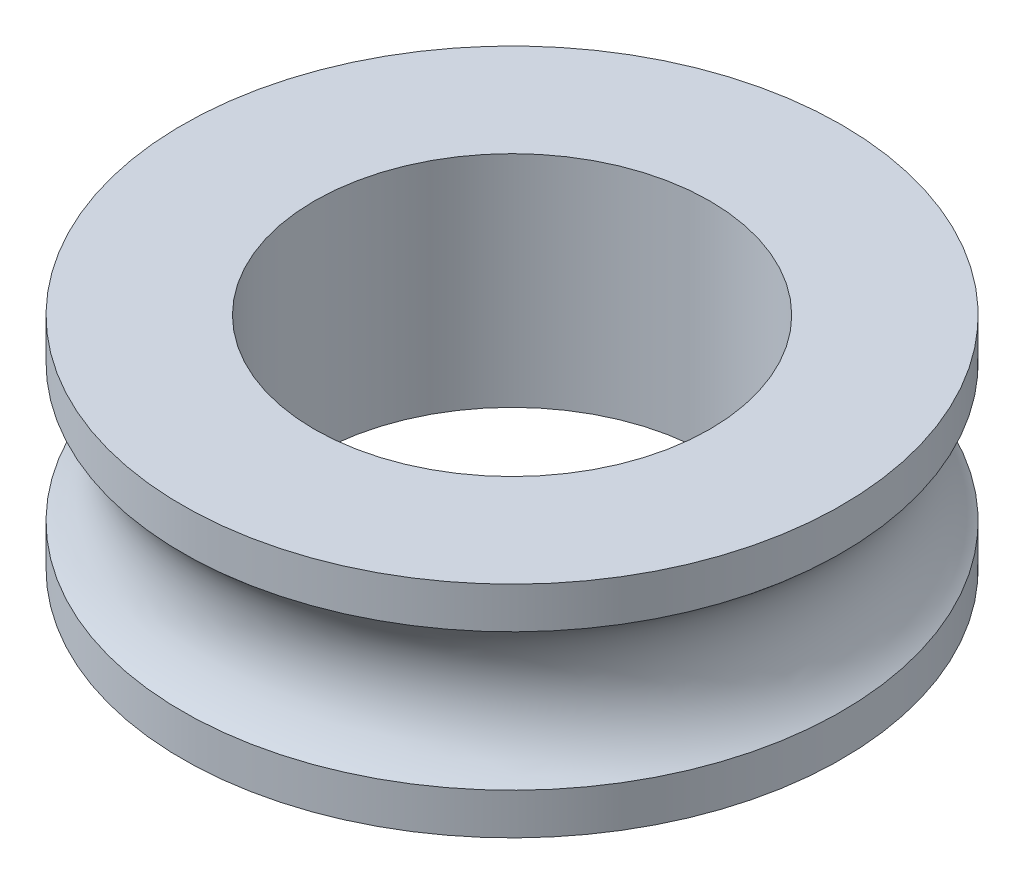
SolidWorks part; units mm, degrees
ref_plane "Ön Düzlem" through (0, 0, 0) normal (0, 0, 1) x (1, 0, 0)
ref_plane "Üst Düzlem" through (0, 0, 0) normal (0, 1, 0) x (1, 0, 0)
ref_plane "Sağ Düzlem" through (0, 0, 0) normal (1, 0, 0) x (0, 0, -1)
sketch "Çizim1" plane through (0, 0, 0) normal (0, 0, 1) x (1, 0, 0)
  line L0 (0, 0) -> (0, 0.5)
  line L1 (0, 0.5) -> (1.5, 0.5)
  line L2 (1.5, -0.5) -> (0, -0.5)
  line L3 (0, -0.5) -> (0, 0)
  line L4 (1.5, 0.5) -> (1.5, 0.3122)
  line L5 (0, 0) -> (1.5, -0.5) construction
  line L6 (0, 0) -> (1.5, 0.5) construction
  line L7 (1.5, -0.3122) -> (1.5, -0.5)
  arc A0 (1.5, 0.3122) -> (1.5, -0.3122) centre (1.75, 0) ccw
  point P0 (0, 0)
  point P8 (0, 0)
  dimension "D6" = 0.8
  dimension "D1" = 1
  dimension "D2" = 1.5
  dimension "D3" = 1.75
  dimension "D4" = 0.5
revolve "Döndür1" add sketch "Çizim1" angle 360 about L0
sketch "Çizim2" plane through (0, 0.5, 0) normal (0, 1, 0) x (1, 0, 0)
  circle A0 centre (0, 0) radius 0.9
  dimension "D1" = 1.8
extrude "Kes-Ekstrüzyon1" cut sketch "Çizim2" against normal blind 1
